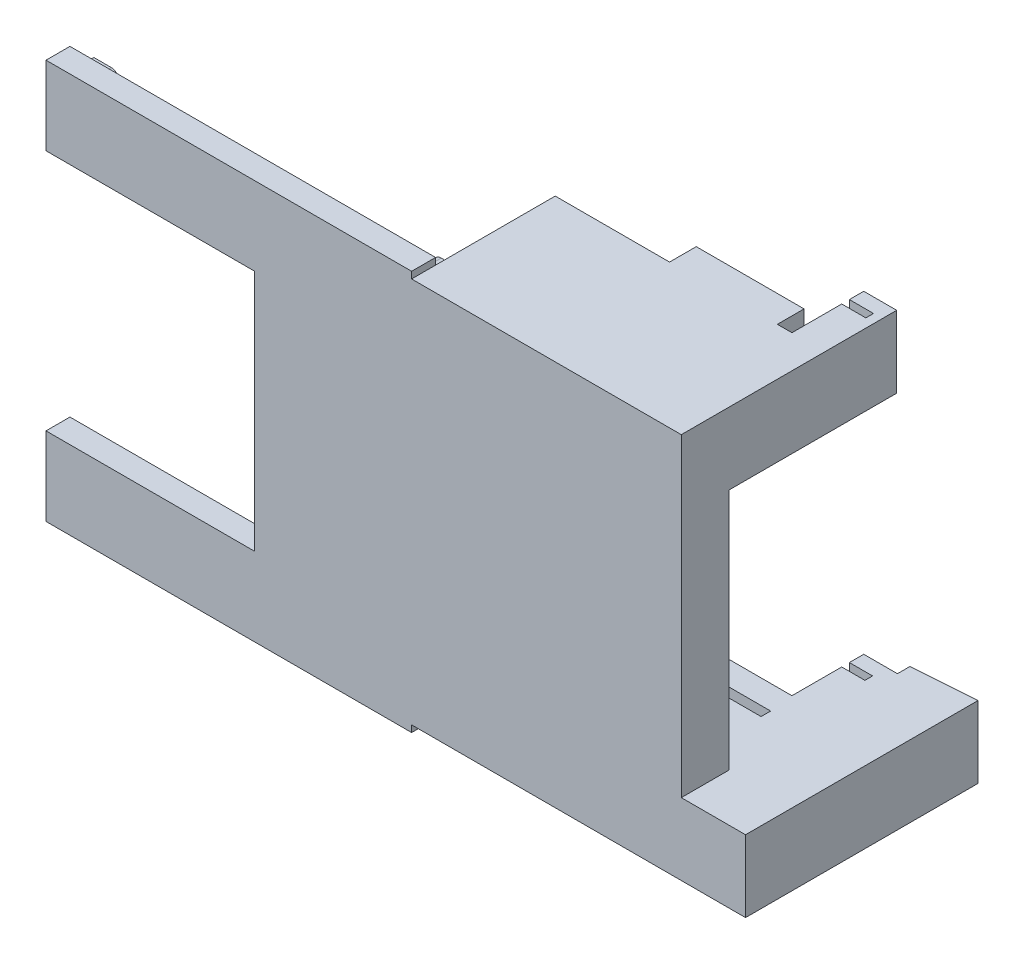
SolidWorks part; units mm, degrees
ref_plane "Front Plane" through (0, 0, 0) normal (0, 0, 1) x (1, 0, 0)
ref_plane "Top Plane" through (0, 0, 0) normal (0, 1, 0) x (1, 0, 0)
ref_plane "Right Plane" through (0, 0, 0) normal (1, 0, 0) x (0, 0, -1)
sketch "Sketch2" plane through (0, 0, 0) normal (0, 0, 1) x (1, 0, 0)
  line L1 (-57.9461, 36.6943) -> (55.249, 36.6943)
  line L2 (-57.9461, 36.6943) -> (-57.9461, -27.6552)
  line L3 (-57.9461, -27.6552) -> (55.249, -27.6552)
  line L4 (55.249, 36.6943) -> (55.249, -27.6552)
  point P0 (0, 0)
extrude "Boss-Extrude1" add sketch "Sketch2" along normal blind 6.35
sketch "Sketch5" plane through (0, 0, 0) normal (0, 0, -1) x (-1, 0, 0)
  line L0 (57.9461, 4.5195) -> (-50.0517, 4.5195) construction
  line L1 (57.9461, 36.6943) -> (57.9461, -27.6552) construction
sketch "Sketch6" plane through (0, 0, 6.35) normal (0, 0, 1) x (1, 0, 0)
  line L0 (-16.2971, 36.6943) -> (-16.2971, 55.7443)
  line L1 (55.249, 36.6943) -> (-57.9461, 36.6943) construction
  line L2 (-16.2971, 55.7443) -> (55.249, 55.7443)
  line L3 (55.249, 55.7443) -> (55.249, 36.6943)
  line L4 (-16.2971, 36.6943) -> (55.249, 36.6943)
  line L5 (-13.7571, -40.5366) -> (-13.7571, 48.3634) construction
  line L6 (-16.2971, -27.6552) -> (-16.2971, -46.7052)
  line L7 (-57.9461, -27.6552) -> (55.249, -27.6552) construction
  line L8 (-16.2971, -46.7052) -> (55.249, -46.7052)
  line L9 (55.249, -46.7052) -> (55.249, -27.6552)
  line L10 (55.249, -27.6552) -> (-16.2971, -27.6552)
  dimension "D1" = 2.54
  dimension "D2" = 19.05
  dimension "D3" = 19.05
extrude "Boss-Extrude4" add sketch "Sketch6" against normal blind 38.1
sketch "Sketch8" plane through (-16.2971, 0, 0) normal (-1, 0, 0) x (0, 0, 1)
  line L1 (-25.4, 53.2043) -> (-22.86, 53.2043)
  line L2 (-25.4, 53.2043) -> (-25.4, 36.6943)
  line L3 (-25.4, 36.6943) -> (-22.86, 36.6943)
  line L4 (-22.86, 53.2043) -> (-22.86, 36.6943)
  line L5 (-31.75, 36.6943) -> (0, 36.6943) construction
  line L6 (-31.75, 55.7443) -> (-31.75, 36.6943) construction
  line L8 (-31.75, -27.6552) -> (0, -27.6552) construction
  line L9 (-25.4, -27.6552) -> (-22.86, -27.6552)
  line L10 (-25.4, -27.6552) -> (-25.4, -44.1652)
  line L11 (-25.4, -44.1652) -> (-22.86, -44.1652)
  line L12 (-22.86, -27.6552) -> (-22.86, -44.1652)
  line L13 (-31.75, -27.6552) -> (-31.75, -46.7052) construction
  dimension "D1" = 2.54
  dimension "D2" = 16.51
  dimension "D3" = 6.35
  dimension "D4" = 2.54
  dimension "D5" = 6.35
  dimension "D6" = 16.51
extrude "Cut-Extrude1" cut sketch "Sketch8" against normal blind 63.5
sketch "Sketch9" plane through (0, 0, -31.75) normal (0, 0, -1) x (-1, 0, 0)
  circle A0 centre (4.791, -40.3952) radius 1.27
  circle A1 centre (-50.209, -40.3952) radius 1.27
  circle A2 centre (-50.209, 52.6048) radius 1.27
  circle A3 centre (4.791, 52.6048) radius 1.27
  dimension "D1" = 2.54
sketch "Sketch11" plane through (0, 0, 6.35) normal (0, 0, 1) x (1, 0, 0)
  line L1 (-16.2971, 36.6943) -> (-113.2971, 36.6943)
  line L2 (-16.2971, 36.6943) -> (-16.2971, 57.5143)
  line L3 (-16.2971, 57.5143) -> (-113.2971, 57.5143)
  line L4 (-113.2971, 36.6943) -> (-113.2971, 57.5143)
  line L5 (-16.2971, -27.6552) -> (-113.2971, -27.6552)
  line L6 (-16.2971, -27.6552) -> (-16.2971, -48.4752)
  line L7 (-16.2971, -48.4752) -> (-113.2971, -48.4752)
  line L8 (-113.2971, -27.6552) -> (-113.2971, -48.4752)
extrude "Boss-Extrude8" add sketch "Sketch11" along a picked direction on the side against the normal blind 6.35
sketch "Sketch16" plane through (0, 0, 0) normal (0, 0, -1) x (-1, 0, 0)
  line L0 (16.2971, 55.7443) -> (16.2971, 36.6943) construction
  line L1 (16.2971, 51.7823) -> (21.1231, 51.7823)
  line L2 (16.2971, 51.7823) -> (16.2971, 47.7183)
  line L3 (16.2971, 47.7183) -> (21.1231, 47.7183)
  line L5 (21.2971, 47.4643) -> (16.2971, 47.4643) construction
  arc A0 (21.1231, 47.7183) -> (21.1231, 51.7823) centre (21.1231, 49.7503) ccw
  dimension "D3" = 2.032
  dimension "D1" = 4.064
  dimension "D2" = 0.254
  dimension "D4" = 4.826
sketch "Sketch17" plane through (0, 0, 0) normal (0, 0, -1) x (-1, 0, 0)
  line L1 (16.2971, -38.6072) -> (21.1231, -38.6072)
  line L2 (16.2971, -38.6072) -> (16.2971, -42.6712)
  line L3 (16.2971, -42.6712) -> (21.1231, -42.6712)
  line L6 (16.2971, -27.6552) -> (16.2971, -46.7052) construction
  line L7 (16.2971, -42.9252) -> (21.2971, -42.9252) construction
  arc A0 (21.1231, -42.6712) -> (21.1231, -38.6072) centre (21.1231, -40.6392) ccw
  dimension "D3" = 2.032
  dimension "D1" = 4.064
  dimension "D2" = 0.254
  dimension "D4" = 4.826
extrude "Boss-Extrude13" add sketch "Sketch16" along normal blind 6.35
extrude "Boss-Extrude14" add sketch "Sketch17" along normal blind 6.35
sketch "Sketch18" plane through (0, 0, 0) normal (0, 0, -1) x (-1, 0, 0)
  line L0 (113.2971, 36.6943) -> (113.2971, 57.5143) construction
  line L1 (113.2971, 51.7823) -> (108.6966, 51.7823)
  line L2 (113.2971, 51.7823) -> (113.2971, 47.7183)
  line L3 (113.2971, 47.7183) -> (108.6966, 47.7183)
  line L5 (108.2971, 47.4643) -> (113.2971, 47.4643) construction
  arc A0 (108.6966, 51.7823) -> (108.6966, 47.7183) centre (108.6966, 49.7503) ccw
  dimension "D4" = 2.032
  dimension "D1" = 4.064
  dimension "D2" = 0.254
extrude "Boss-Extrude15" add sketch "Sketch18" along normal blind 6.35
sketch "Sketch19" plane through (0, 0, 0) normal (0, 0, -1) x (-1, 0, 0)
  line L1 (113.2971, -38.6072) -> (108.6966, -38.6072)
  line L2 (113.2971, -38.6072) -> (113.2971, -42.6712)
  line L3 (113.2971, -42.6712) -> (108.6966, -42.6712)
  line L6 (113.2971, -48.4752) -> (113.2971, -27.6552) construction
  line L7 (113.2971, -42.9252) -> (108.2971, -42.9252) construction
  arc A0 (108.6966, -38.6072) -> (108.6966, -42.6712) centre (108.6966, -40.6392) ccw
  dimension "D4" = 2.032
  dimension "D1" = 4.064
  dimension "D2" = 0.254
extrude "Boss-Extrude16" add sketch "Sketch19" along normal blind 6.35 contours A0 L3 L2 L1
sketch "Sketch20" plane through (0, 0, -31.75) normal (0, 0, -1) x (-1, 0, 0)
  line L1 (-55.249, -27.6552) -> (-72.2948, -27.6552)
  line L2 (-55.249, -27.6552) -> (-55.249, -46.7052)
  line L3 (-55.249, -46.7052) -> (-72.2948, -46.7052)
  line L4 (-72.2948, -27.6552) -> (-72.2948, -46.7052)
extrude "Boss-Extrude17" add sketch "Sketch20" against normal up to surface (38.1 mm away) up to face at (-43.6476, 4.5195, 6.35)
sketch "Sketch21" plane through (0, 0, -31.75) normal (0, 0, -1) x (-1, 0, 0)
  line L0 (-55.4452, -27.6552) -> (-55.5749, -30.2894)
  line L1 (-72.2948, -27.6552) -> (16.2971, -27.6552) construction
  line L2 (-55.5749, -30.2894) -> (-67.7452, -30.2894)
  line L3 (-67.7452, -30.2894) -> (-67.7452, -44.0894)
  line L4 (-67.7452, -44.0894) -> (-55.5749, -44.0894)
  line L5 (-55.5749, -44.0894) -> (-55.5749, -46.7052)
  line L6 (16.2971, -46.7052) -> (-72.2948, -46.7052) construction
  line L7 (-55.5749, -46.7052) -> (-72.2948, -46.7052)
  line L8 (-72.2948, -46.7052) -> (-72.2948, -27.6552)
  line L9 (-72.2948, -27.6552) -> (-55.4452, -27.6552)
extrude "Boss-Extrude18" add sketch "Sketch21" along normal up to surface (23.5728 mm away)
sketch "Sketch22" plane through (0, -30.2894, 0) normal (0, -1, 0) x (1, 0, 0)
  line L5 (55.5749, -54.1537) -> (55.5749, -31.75) construction
  line L6 (55.5749, -47.3165) -> (56.8256, -47.3165)
  line L7 (55.5749, -47.3165) -> (55.5749, -54.1537)
  line L9 (56.8256, -47.3165) -> (56.8256, -54.1537)
  line L10 (56.8256, -54.1537) -> (56.8195, -54.2407)
  line L11 (67.7452, -55.0047) -> (55.5749, -54.1537) construction
  line L12 (56.8195, -54.2407) -> (55.5749, -54.1537)
extrude "Boss-Extrude19" add sketch "Sketch22" along normal up to surface (13.8 mm away) up to face at (61.6601, -44.0894, -43.1646)
sketch "Sketch23" plane through (0, 0, -31.75) normal (0, 0, -1) x (-1, 0, 0)
  line L0 (-0.8565, -46.7052) -> (-0.8565, -27.6552)
  line L1 (-55.249, 55.7443) -> (-46.5051, 55.7443)
  line L2 (-55.249, 55.7443) -> (-55.249, 36.6943)
  line L3 (-55.249, 36.6943) -> (-46.5051, 36.6943)
  line L5 (16.2971, -27.6552) -> (-0.8565, -27.6552)
  line L6 (16.2971, -27.6552) -> (16.2971, -46.7052)
  line L7 (16.2971, -46.7052) -> (-0.8565, -46.7052)
  line L8 (-55.5749, -27.6552) -> (-55.5749, -46.7052)
  line L9 (-46.5051, -46.7052) -> (-46.5051, -27.6552)
  line L10 (-46.5051, -46.7052) -> (-55.5749, -46.7052)
  line L11 (-46.5051, -27.6552) -> (-55.5749, -27.6552)
  line L13 (-46.5051, 36.6943) -> (-46.5051, 55.7443)
extrude "Boss-Extrude20" add sketch "Sketch23" along normal blind 19.05
sketch "Sketch24" plane through (0, -27.6552, 0) normal (0, 1, 0) x (1, 0, 0)
  line L0 (0.8565, 50.8) -> (0.8565, 31.75) construction
  line L1 (0.8565, 44.958) -> (-7.6825, 44.958)
  line L2 (0.8565, 44.958) -> (0.8565, 46.99)
  line L3 (0.8565, 46.99) -> (-7.6825, 46.99)
  line L4 (-7.6825, 44.958) -> (-7.6825, 46.99)
  line L5 (46.5051, 50.8) -> (46.5051, 31.75) construction
  line L6 (52.6615, 46.99) -> (46.5051, 46.99)
  line L7 (52.6615, 46.99) -> (52.6615, 44.958)
  line L8 (52.6615, 44.958) -> (46.5051, 44.958)
  line L9 (46.5051, 46.99) -> (46.5051, 44.958)
  line L10 (-16.2971, 50.8) -> (0.8565, 50.8) construction
  line L11 (46.5051, 50.8) -> (55.249, 50.8) construction
  dimension "D1" = 2.032
  dimension "D2" = 2.032
  dimension "D3" = 3.81
  dimension "D4" = 3.81
extrude "Cut-Extrude2" cut sketch "Sketch24" along direction (0, -1, 0) on the side against the normal blind 15.748
sketch "Sketch25" plane through (0, 36.6943, 0) normal (0, -1, 0) x (1, 0, 0)
  line L0 (46.5051, -50.8) -> (46.5051, -31.75) construction
  line L1 (52.9099, -46.99) -> (46.5051, -46.99)
  line L2 (52.9099, -46.99) -> (52.9099, -44.958)
  line L3 (52.9099, -44.958) -> (46.5051, -44.958)
  line L4 (46.5051, -46.99) -> (46.5051, -44.958)
  line L5 (55.5749, -50.8) -> (46.5051, -50.8) construction
  dimension "D1" = 3.81
  dimension "D2" = 2.032
extrude "Cut-Extrude3" cut sketch "Sketch25" against normal through all
sketch "Sketch26" plane through (0, 0, -31.75) normal (0, 0, -1) x (-1, 0, 0)
  line L0 (16.2971, 36.6943) -> (-46.5051, 36.6943) construction
  line L1 (-14.0333, 36.6943) -> (-42.6368, 36.6943)
  line L2 (-14.0333, 36.6943) -> (-14.0333, 55.7443)
  line L3 (-14.0333, 55.7443) -> (-42.6368, 55.7443)
  line L4 (-42.6368, 36.6943) -> (-42.6368, 55.7443)
  line L5 (-46.5051, 55.7443) -> (16.2971, 55.7443) construction
extrude "Boss-Extrude21" add sketch "Sketch26" along normal up to surface (7.0851 mm away)
sketch "Sketch27" plane through (0, 0, 0) normal (0, 0, -1) x (-1, 0, 0)
  line L0 (-46.4479, 30.5257) -> (-50.0039, 26.9697) construction
  line L1 (-55.249, 36.6943) -> (-47.1459, 36.6943)
  line L2 (-55.249, 36.6943) -> (-55.249, -27.6552)
  line L3 (-55.249, -27.6552) -> (-47.1459, -27.6552)
  line L4 (-47.1459, 36.6943) -> (-47.1459, 36.5602)
  line L5 (-47.1459, 29.8277) -> (27.2243, 29.8277)
  line L7 (-47.1459, 36.5602) -> (27.2243, 36.5602)
  line L8 (27.2243, 29.8277) -> (27.2243, 36.5602)
  line L9 (-47.1459, 29.8277) -> (-47.1459, -22.1068)
  line L10 (16.2971, -27.6552) -> (-0.8565, -27.6552) construction
  line L11 (-47.1459, -22.1068) -> (30.256, -22.1068)
  line L13 (-47.1459, -27.6552) -> (30.256, -27.6552)
  line L14 (30.256, -22.1068) -> (30.256, -27.6552)
extrude "Boss-Extrude22" add sketch "Sketch27" along normal blind 6.35
sketch "Sketch30" plane through (47.1459, 0, 0) normal (-1, 0, 0) x (0, 0, 1)
  line L1 (-4.4462, 31.0781) -> (-1.9062, 31.0781)
  line L2 (-4.4462, 31.0781) -> (-4.4462, -23.4274)
  line L3 (-4.4462, -23.4274) -> (-1.9062, -23.4274)
  line L4 (-1.9062, 31.0781) -> (-1.9062, -23.4274)
  dimension "D1" = 2.54
extrude "Cut-Extrude4" cut sketch "Sketch30" against normal up to vertex (2.9057 mm away) and the other way blind 77.978 up to point (50.0517, 4.5195, 0)
sketch "Sketch32" plane through (46.5051, 0, 0) normal (-1, 0, 0) x (0, 0, 1)
  line L0 (-31.75, -46.7052) -> (-31.75, -27.6552) construction
  line L1 (-31.75, -45.0475) -> (-39.0075, -45.0475)
  line L2 (-31.75, -45.0475) -> (-31.75, -29.9294)
  line L3 (-31.75, -29.9294) -> (-39.0075, -29.9294)
  line L4 (-39.0075, -45.0475) -> (-39.0075, -29.9294)
extrude "Cut-Extrude5" cut sketch "Sketch32" against normal blind 21.59
